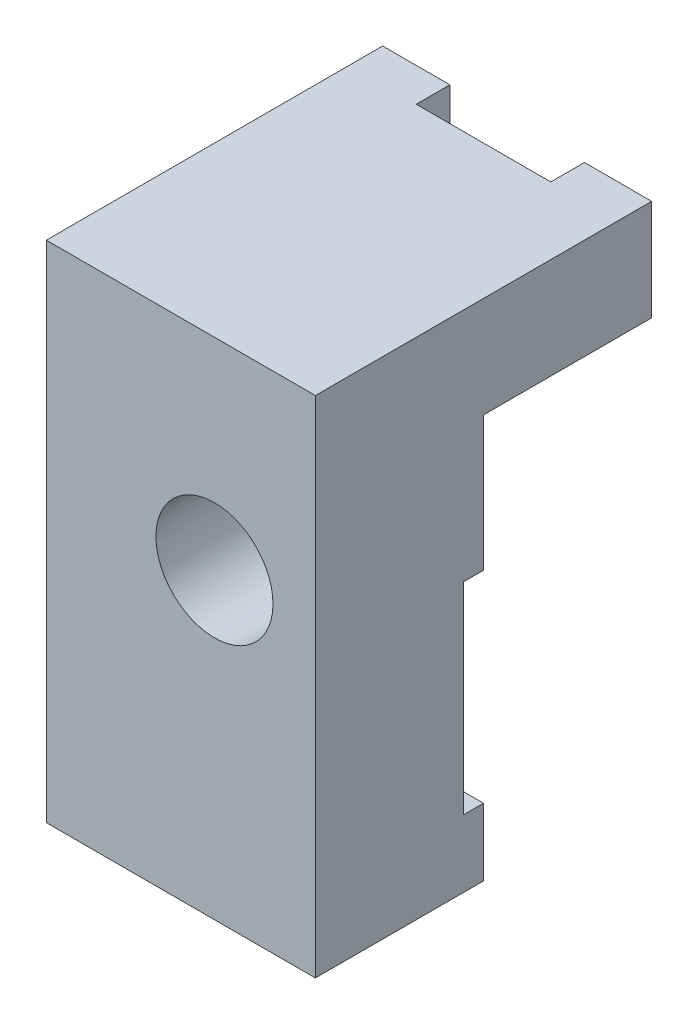
SolidWorks part; units mm, degrees
ref_plane "Front Plane" through (0, 0, 0) normal (0, 0, 1) x (1, 0, 0)
ref_plane "Top Plane" through (0, 0, 0) normal (0, 1, 0) x (1, 0, 0)
ref_plane "Right Plane" through (0, 0, 0) normal (1, 0, 0) x (0, 0, -1)
sketch "Sketch1" plane through (0, 0, 0) normal (0, 0, 1) x (1, 0, 0)
  line L1 (-5.08, 9.525) -> (5.08, 9.525)
  line L2 (-5.08, 9.525) -> (-5.08, -9.525)
  line L3 (-5.08, -9.525) -> (5.08, -9.525)
  line L4 (5.08, 9.525) -> (5.08, -9.525)
  dimension "D1" = 5.08
  dimension "D2" = 5.08
  dimension "D3" = 9.525
  dimension "D4" = 9.525
extrude "Boss-Extrude1" add sketch "Sketch1" along normal mid plane 12.7
sketch "Sketch2" plane through (5.08, 0, 0) normal (1, 0, 0) x (0, 0, -1)
  line L0 (-6.35, 9.525) -> (6.35, 9.525) construction
  line L1 (6.35, -9.525) -> (0, -9.525)
  line L2 (6.35, -9.525) -> (6.35, 5.715)
  line L3 (6.35, 5.715) -> (0, 5.715)
  line L4 (0, -9.525) -> (0, 5.715)
  dimension "D1" = 6.35
  dimension "D2" = 3.81
extrude "Cut-Extrude1" cut sketch "Sketch2" against normal through all
sketch "Sketch3" plane through (0, 9.525, 0) normal (0, 1, 0) x (1, 0, 0)
  line L0 (5.08, 6.35) -> (-5.08, 6.35) construction
  line L1 (-2.54, 6.35) -> (2.54, 6.35)
  line L2 (-2.54, 6.35) -> (-2.54, 5.08)
  line L3 (-2.54, 5.08) -> (2.54, 5.08)
  line L4 (2.54, 6.35) -> (2.54, 5.08)
  line L5 (5.08, -6.35) -> (5.08, 6.35) construction
  line L6 (-5.08, -6.35) -> (-5.08, 6.35) construction
  dimension "D1" = 2.54
  dimension "D2" = 2.54
  dimension "D3" = 1.27
extrude "Cut-Extrude2" cut sketch "Sketch3" against normal through all
sketch "Sketch4" plane through (5.08, 0, 0) normal (1, 0, 0) x (0, 0, -1)
  line L0 (0, 5.715) -> (0, -9.525) construction
  line L1 (0, -6.985) -> (-0.762, -6.985)
  line L2 (0, -6.985) -> (0, 0.635)
  line L3 (0, 0.635) -> (-0.762, 0.635)
  line L4 (-0.762, -6.985) -> (-0.762, 0.635)
  line L5 (-6.35, -9.525) -> (0, -9.525) construction
  dimension "D1" = 2.54
  dimension "D2" = 0.762
  dimension "D3" = 7.62
extrude "Cut-Extrude3" cut sketch "Sketch4" against normal through all
sketch "Sketch5" plane through (0, 0, 6.35) normal (0, 0, 1) x (1, 0, 0)
  line L0 (5.08, -9.525) -> (5.08, 9.525) construction
  line L1 (-5.08, -9.525) -> (5.08, -9.525) construction
  circle A0 centre (1.27, 1.905) radius 2.2098
  dimension "D1" = 3.81
  dimension "D2" = 11.43
extrude "Cut-Extrude4" cut sketch "Sketch5" against normal through all
